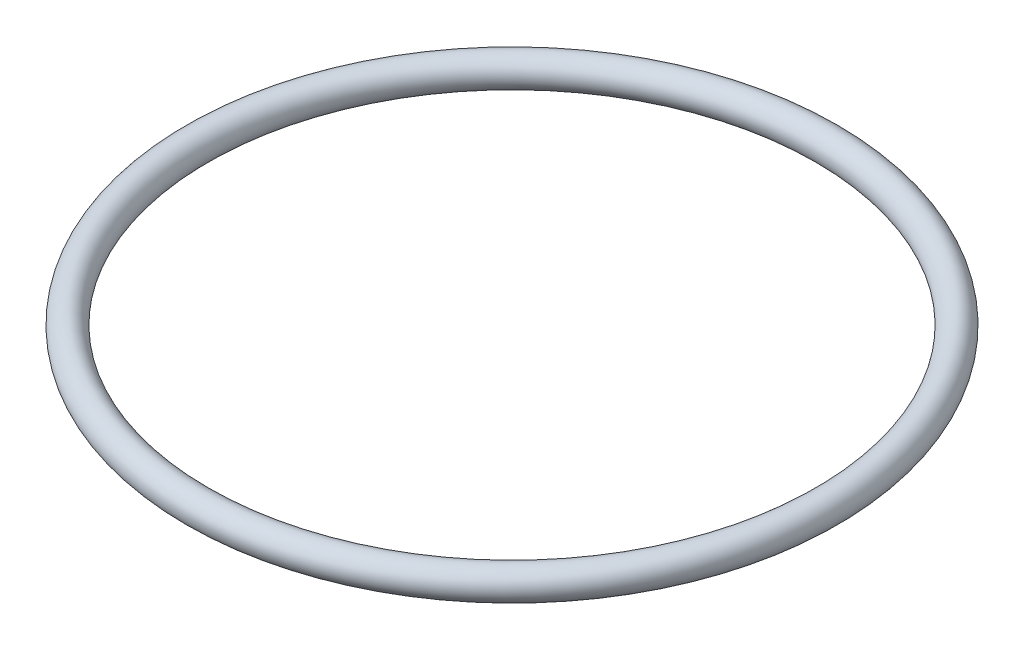
SolidWorks part; units mm, degrees
ref_plane "Piano frontale" through (0, 0, 0) normal (0, 0, 1) x (1, 0, 0)
ref_plane "Piano superiore" through (0, 0, 0) normal (0, 1, 0) x (1, 0, 0)
ref_plane "Piano destro" through (0, 0, 0) normal (1, 0, 0) x (0, 0, -1)
sketch "Schizzo1" plane through (0, 0, 0) normal (0, 0, 1) x (1, 0, 0)
  line L1 (-1.052, 0) -> (-1.052, 5.9263) construction
  line L2 (19.648, 0) -> (-1.052, 0) construction
  circle A1 centre (19.648, 0) radius 1
  dimension "D2" = 2
  dimension "D1" = 20.7
revolve "Rivoluzione1" add sketch "Schizzo1" angle 360 about L1
